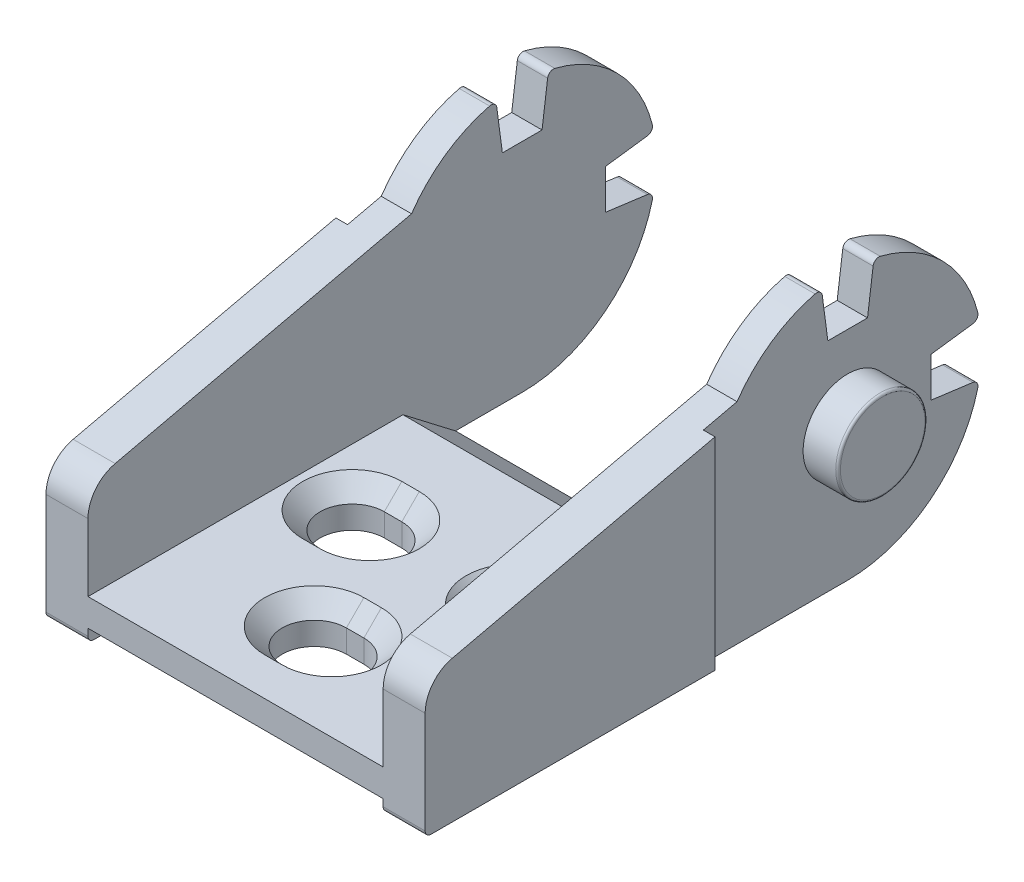
SolidWorks part; units mm, degrees
material "ABS"
ref_plane "Front" through (0, 0, 0) normal (0, 0, 1) x (1, 0, 0)
ref_plane "Top" through (0, 0, 0) normal (0, 1, 0) x (1, 0, 0)
ref_plane "Right" through (0, 0, 0) normal (1, 0, 0) x (0, 0, -1)
sketch "Sketch1" plane through (0, 0, 0) normal (1, 0, 0) x (0, 0, -1)
  line L0 (0, 0) -> (37.2223, 0)
  line L1 (0, 0) -> (0, 11.6268)
  line L2 (0, 11.6268) -> (27.7354, 18)
  line L3 (48.7223, 11.5) -> (37.2223, 11.5) construction
  line L4 (37.2223, 11.5) -> (37.2223, 23) construction
  line L5 (44.35, 9.8) -> (44.35, 13.2)
  line L6 (44.35, 13.2) -> (48.5, 13.75)
  line L7 (3.8, 0) -> (3.8, 12.5) construction
  line L8 (44.35, 9.8) -> (48.5, 9.25)
  line L9 (34.9723, 22.7777) -> (39.4723, 22.7777) construction
  line L10 (48.5, 13.75) -> (48.5, 9.25) construction
  line L14 (35.5223, 18.6277) -> (34.9723, 22.7777)
  line L15 (38.9223, 18.6277) -> (35.5223, 18.6277)
  line L16 (38.9223, 18.6277) -> (39.4723, 22.7777)
  circle A0 centre (37.2223, 11.5) radius 11.5 construction
  arc A1 (27.7354, 18) -> (34.9723, 22.7777) centre (37.2223, 11.5) cw
  arc A2 (48.5, 13.75) -> (39.4723, 22.7777) centre (37.2223, 11.5) ccw
  arc A3 (48.5, 9.25) -> (37.2223, 0) centre (37.2223, 11.5) cw
  point P15 (44.35, 11.5)
  point P16 (37.2223, 18.6277)
  point P26 (37.2223, 11.5)
  dimension "D1" = 23
  dimension "D2" = 4.5
  dimension "D3" = 3.4
  dimension "D4" = 48.5
  dimension "D5" = 18
  dimension "D6" = 3.8
  dimension "D7" = 12.5
  dimension "D8" = 4.15
extrude "Boss-Extrude1" add sketch "Sketch1" along normal mid plane 32.5
sketch "Sketch2" plane through (16.25, 0, 0) normal (1, 0, 0) x (0, 0, -1)
  line L0 (24.85, 17.337) -> (24.85, 0)
  line L1 (27.7354, 18) -> (0, 11.6268) construction
  line L2 (0, 0) -> (37.2223, 0) construction
  line L3 (0, 11.6268) -> (0, 0) construction
  line L4 (24.85, 17.337) -> (24.85, 22.7777)
  line L7 (24.85, 22.7777) -> (48.5, 22.7777)
  line L9 (48.5, 22.7777) -> (48.5, 0)
  line L10 (48.5, 0) -> (24.85, 0)
  dimension "D1" = 24.85
extrude "Cut-Extrude1" cut sketch "Sketch2" against normal blind 1
sketch "Sketch3" plane through (15.25, 0, 0) normal (1, 0, 0) x (0, 0, -1)
  circle A0 centre (37.2223, 11.5) radius 3.825
  dimension "D1" = 7.65
extrude "Boss-Extrude2" add sketch "Sketch3" along normal blind 3
mirror "Mirror1" about plane through (0, 0, 0) normal (1, 0, 0) of "Cut-Extrude1", "Boss-Extrude2"
ref_plane "Plane1" through (12.65, 0, 0) normal (1, 0, 0) x (0, 0, -1)
sketch "Sketch4" plane through (12.65, 0, 0) normal (1, 0, 0) x (0, 0, -1)
  line L0 (0, 1.1) -> (1.35, 1.1)
  line L1 (0, 11.6268) -> (0, 0) construction
  line L2 (1.35, 1.1) -> (1.35, 2.7)
  line L3 (1.35, 2.7) -> (2.65, 2.7)
  line L4 (2.65, 2.7) -> (2.65, 0)
  line L5 (0, 0) -> (24.85, 0) construction
  line L6 (2.65, 0) -> (0, 0)
  line L7 (0, 0) -> (0, 1.1)
  line L8 (0, 3.45) -> (27, 3.45)
  line L9 (27, 3.45) -> (31.5, 0)
  line L10 (24.85, 0) -> (37.2223, 0) construction
  line L11 (31.5, 0) -> (48.5, 0)
  line L12 (48.5, 0) -> (48.5, 22.7777)
  line L13 (48.5, 22.7777) -> (0, 22.7777)
  line L14 (0, 22.7777) -> (0, 3.45)
  line L15 (34.9723, 22.7777) -> (39.4723, 22.7777) construction
  dimension "D1" = 1.1
  dimension "D2" = 2.7
  dimension "D3" = 2.65
  dimension "D4" = 1.35
  dimension "D5" = 3.45
  dimension "D6" = 31.5
  dimension "D7" = 27
extrude "Cut-Extrude2" cut sketch "Sketch4" against normal offset from surface (25.3 mm away) 3.6 up to face at (-16.25, 7.2409, -12.425)
fillet "Fillet1" radius 0.2 2 edges at (18.25, 11.5, -41.0473) (-18.25, 11.5, -41.0473)
fillet "Fillet2" radius 0.5 10 edges at (14.45, 0, 0) (-14.45, 0, 0) (-13.95, 13.75, -48.5) (-13.95, 9.25, -48.5) (13.95, 9.25, -48.5) (13.95, 13.75, -48.5) (13.95, 22.7777, -34.9723) (13.95, 22.7777, -39.4723) (-13.95, 22.7777, -34.9723) (-13.95, 22.7777, -39.4723)
fillet "Fillet3" radius 3 2 edges at (14.45, 11.6268, 0) (-14.45, 11.6268, 0)
sketch "Sketch5" plane through (0, 3.45, 0) normal (0, 1, 0) x (1, 0, 0)
  line L0 (0, 31.5) -> (0, 0) construction
  line L1 (-12.65, 31.5) -> (12.65, 31.5) construction
  line L2 (-0.75, 7.5) -> (0.75, 7.5) construction
  line L3 (-12.65, 0) -> (12.65, 0) construction
  line L4 (-0.75, 4.75) -> (0.75, 4.75)
  line L5 (-0.75, 10.25) -> (0.75, 10.25)
  line L6 (3.5, 17.75) -> (10.5, 17.75) construction
  line L7 (7, 17.75) -> (7, 0) construction
  line L8 (7.75, 17.75) -> (6.25, 17.75) construction
  line L9 (7.75, 20.5) -> (6.25, 20.5)
  line L10 (7.75, 15) -> (6.25, 15)
  line L11 (-7.75, 20.5) -> (-6.25, 20.5)
  line L12 (-7.75, 15) -> (-6.25, 15)
  arc A0 (-0.75, 4.75) -> (-0.75, 10.25) centre (-0.75, 7.5) cw
  arc A1 (0.75, 4.75) -> (0.75, 10.25) centre (0.75, 7.5) ccw
  arc A2 (7.75, 20.5) -> (7.75, 15) centre (7.75, 17.75) cw
  arc A3 (6.25, 20.5) -> (6.25, 15) centre (6.25, 17.75) ccw
  arc A4 (-6.25, 20.5) -> (-6.25, 15) centre (-6.25, 17.75) cw
  arc A5 (-7.75, 20.5) -> (-7.75, 15) centre (-7.75, 17.75) ccw
  point P8 (0, 7.5)
  point P21 (7, 17.75)
  dimension "D1" = 1.5
  dimension "D2" = 7.5
  dimension "D5" = 7
  dimension "D6" = 7
  dimension "D7" = 17.75
  dimension "D8" = 2.75
  dimension "D3" = 2.75
  dimension "D4" = 2.75
  dimension "D9" = 2.75
extrude "Cut-Extrude3" cut sketch "Sketch5" against normal through all
chamfer "Chamfer1" distance 1.5 angle 45 12 edges at (-3.5, 3.45, -7.5) (0, 3.45, -4.75) (0, 3.45, -10.25) (3.5, 3.45, -7.5) (10.5, 3.45, -17.75) (7, 3.45, -20.5) (7, 3.45, -15) (3.5, 3.45, -17.75) (-3.5, 3.45, -17.75) (-7, 3.45, -20.5) (-7, 3.45, -15) (-10.5, 3.45, -17.75)
